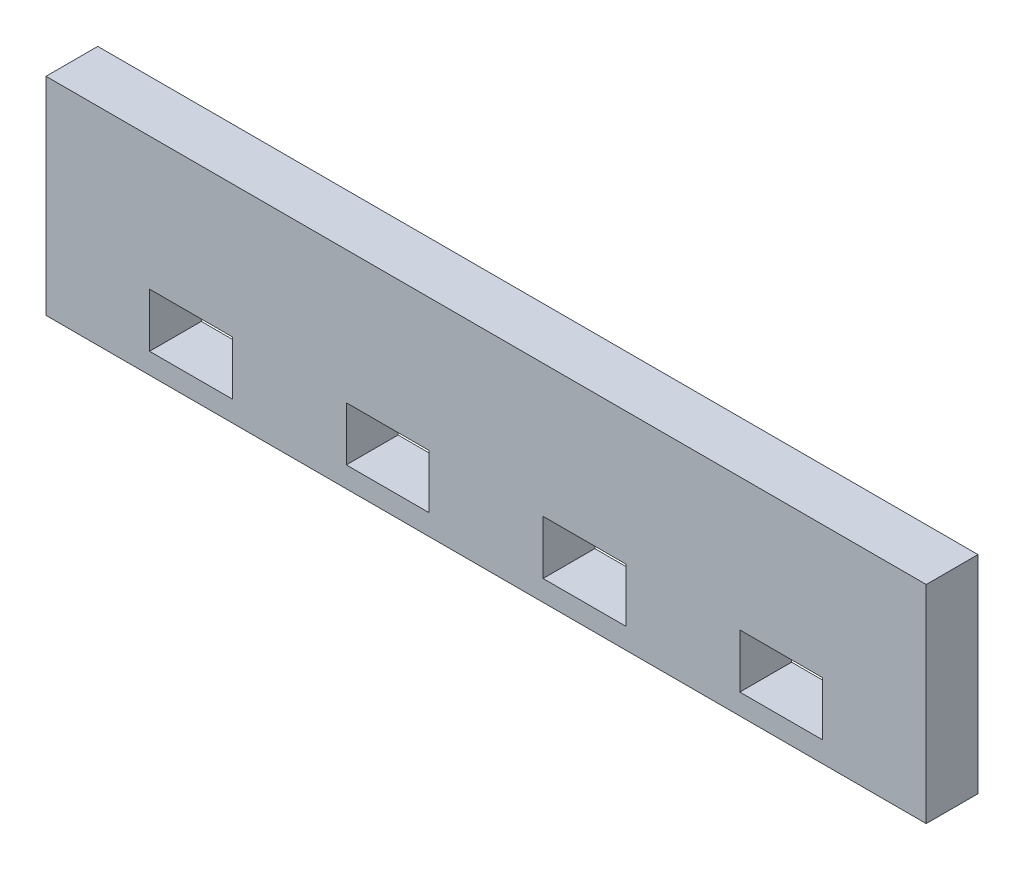
SolidWorks part; units mm, degrees
ref_plane "Front Plane" through (0, 0, 0) normal (0, 0, 1) x (1, 0, 0)
ref_plane "Top Plane" through (0, 0, 0) normal (0, 1, 0) x (1, 0, 0)
ref_plane "Right Plane" through (0, 0, 0) normal (1, 0, 0) x (0, 0, -1)
sketch "Sketch1" plane through (0, 0, 0) normal (0, 0, 1) x (1, 0, 0)
  line L1 (-21.9712, 20) -> (63.0288, 20)
  line L2 (-21.9712, 20) -> (-21.9712, 0)
  line L3 (-21.9712, 0) -> (63.0288, 0)
  line L4 (63.0288, 20) -> (63.0288, 0)
  dimension "D1" = 85
  dimension "D6" = 20
extrude "Boss-Extrude1" add sketch "Sketch1" along normal blind 5 contours L1 L4 L3 L2
sketch "Sketch2" plane through (0, 0, 5) normal (0, 0, 1) x (1, 0, 0)
  line L0 (-1.9712, 4.6) -> (-21.9712, 4.6) construction
  line L1 (-11.9712, 7.2) -> (-3.9712, 7.2)
  line L2 (-11.9712, 7.2) -> (-11.9712, 2)
  line L3 (-11.9712, 2) -> (-3.9712, 2)
  line L4 (-3.9712, 7.2) -> (-3.9712, 2)
  line L5 (-21.9712, 20) -> (-21.9712, 0) construction
  line L6 (7.0288, 7.2) -> (15.0288, 7.2)
  line L7 (7.0288, 7.2) -> (7.0288, 2)
  line L8 (7.0288, 2) -> (15.0288, 2)
  line L9 (15.0288, 7.2) -> (15.0288, 2)
  line L10 (26.0288, 7.2) -> (34.0288, 7.2)
  line L11 (26.0288, 7.2) -> (26.0288, 2)
  line L12 (26.0288, 2) -> (34.0288, 2)
  line L13 (34.0288, 7.2) -> (34.0288, 2)
  line L14 (45.0288, 7.2) -> (53.0288, 7.2)
  line L15 (45.0288, 7.2) -> (45.0288, 2)
  line L16 (45.0288, 2) -> (53.0288, 2)
  line L17 (53.0288, 7.2) -> (53.0288, 2)
  line L18 (-21.9712, 0) -> (63.0288, 0) construction
  point P9 (-11.9712, 4.6)
  point P14 (7.0288, 4.6)
  point P19 (26.0288, 4.6)
  point P24 (45.0288, 4.6)
  dimension "D2" = 5.2
  dimension "D3" = 8
  dimension "D4" = 10
  dimension "D5" = 4.6
  dimension "D6" = 11
  dimension "D1" = 4
extrude "Cut-Extrude1" cut sketch "Sketch2" against normal up to next
